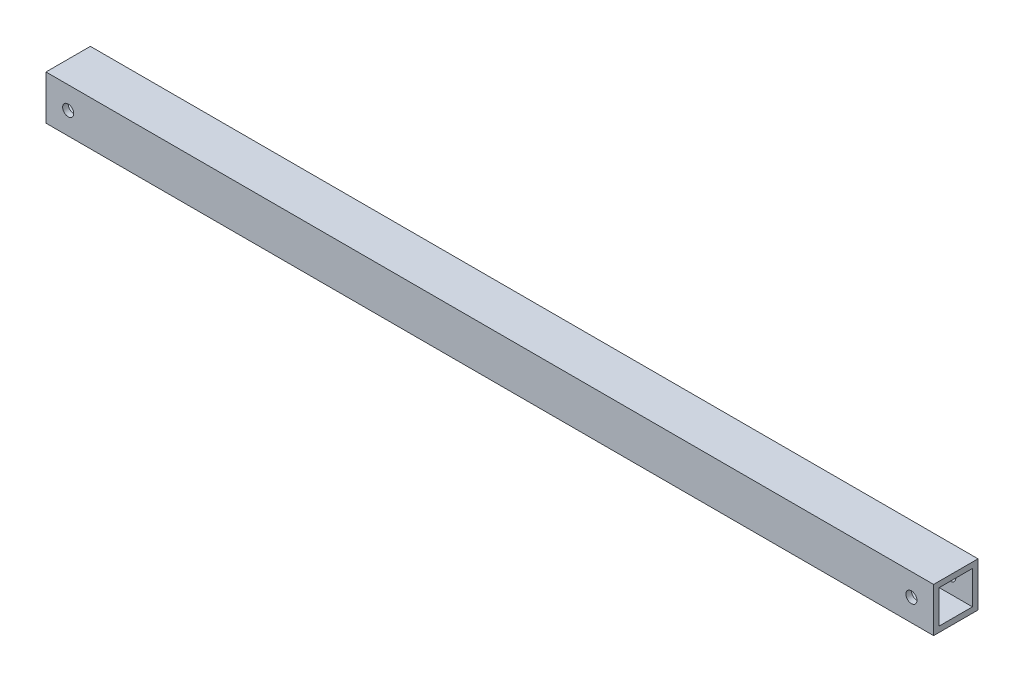
SolidWorks part; units mm, degrees
ref_plane "Front Plane" through (0, 0, 0) normal (0, 0, 1) x (1, 0, 0)
ref_plane "Top Plane" through (0, 0, 0) normal (0, 1, 0) x (1, 0, 0)
ref_plane "Right Plane" through (0, 0, 0) normal (1, 0, 0) x (0, 0, -1)
sketch "Sketch1" plane through (0, 0, 0) normal (0, 0, 1) x (1, 0, 0)
  line L1 (-254, -12.7) -> (254, -12.7)
  line L2 (-254, -12.7) -> (-254, 12.7)
  line L3 (-254, 12.7) -> (254, 12.7)
  line L4 (254, -12.7) -> (254, 12.7)
  line L5 (-254, -12.7) -> (254, 12.7) construction
  line L6 (-254, 12.7) -> (254, -12.7) construction
  point P0 (0, 0)
extrude "Boss-Extrude1" add sketch "Sketch1" along normal blind 25.4
sketch "Sketch2" plane through (254, 0, 0) normal (1, 0, 0) x (0, 0, -1)
  line L0 (-12.7, 12.7) -> (-12.7, -12.7)
  line L1 (-25.4, 12.7) -> (0, 12.7) construction
  line L2 (-25.4, -12.7) -> (0, -12.7) construction
  line L3 (-3.175, 9.5204) -> (-3.175, 12.7)
  line L4 (-22.225, -9.5204) -> (-3.175, -9.5204)
  line L5 (-22.225, -9.5204) -> (-22.225, 9.5204)
  line L6 (-22.225, 9.5204) -> (-3.175, 9.5204)
  line L7 (-3.175, -9.5204) -> (-3.175, 9.5204)
  line L8 (-22.225, -9.5204) -> (-3.175, 9.5204) construction
  line L9 (-22.225, 9.5204) -> (-3.175, -9.5204) construction
  line L10 (-3.175, 9.5204) -> (0, 9.5204)
  line L11 (0, -12.7) -> (0, 12.7) construction
  point P6 (-12.7, 0)
extrude "Cut-Extrude1" cut sketch "Sketch2" against normal blind 508 contours L6 L5 L4 L0 | L4 L7 L6 L0
sketch "Sketch3" plane through (0, 0, 25.4) normal (0, 0, 1) x (1, 0, 0)
  line L0 (254, 0) -> (241.3, 0)
  line L1 (254, -12.7) -> (254, 12.7) construction
  line L2 (-254, 0) -> (-241.3, 0)
  line L3 (-254, 12.7) -> (-254, -12.7) construction
  circle A0 centre (241.3, 0) radius 3.175
  circle A1 centre (-241.3, 0) radius 3.175
extrude "Cut-Extrude2" cut sketch "Sketch3" against normal blind 508
